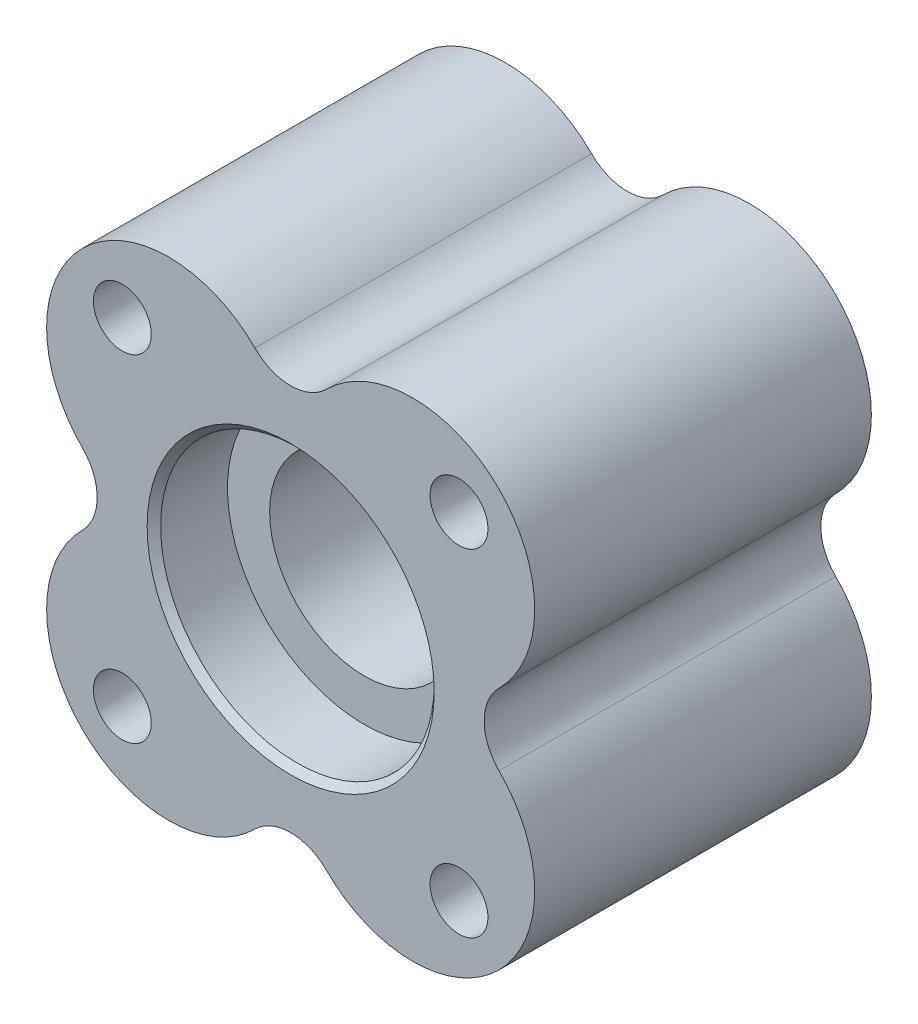
SolidWorks part; units mm, degrees
ref_plane "Front Plane" through (0, 0, 0) normal (0, 0, 1) x (1, 0, 0)
ref_plane "Top Plane" through (0, 0, 0) normal (0, 1, 0) x (1, 0, 0)
ref_plane "Right Plane" through (0, 0, 0) normal (1, 0, 0) x (0, 0, -1)
sketch "Sketch1" plane through (0, 0, 0) normal (0, 0, 1) x (1, 0, 0)
  line L1 (-25.4, 25.4) -> (25.4, 25.4) construction
  line L2 (-25.4, 25.4) -> (-25.4, -25.4) construction
  line L3 (-25.4, -25.4) -> (25.4, -25.4) construction
  line L4 (25.4, 25.4) -> (25.4, -25.4) construction
  line L5 (-25.4, 25.4) -> (25.4, -25.4) construction
  line L6 (-25.4, -25.4) -> (25.4, 25.4) construction
  circle A0 centre (-25.4, 25.4) radius 3.9688
  circle A1 centre (25.4, 25.4) radius 3.9688
  circle A2 centre (25.4, -25.4) radius 3.9688
  circle A3 centre (-25.4, -25.4) radius 3.9688
  circle A4 centre (0, 0) radius 20.6375
  circle A5 centre (0, 0) radius 44.45
  point P0 (0, 0)
  dimension "D3" = 41.275
  dimension "D4" = 7.9375
  dimension "D5" = 88.9
  dimension "D1" = 50.8
  dimension "D2" = 50.8
extrude "Boss-Extrude1" add sketch "Sketch1" along normal mid plane 50.8
sketch "Sketch2" plane through (0, 0, 0) normal (0, 0, 1) x (1, 0, 0)
  circle A0 centre (0, 0) radius 20.6375 construction
  circle A1 centre (0, 0) radius 20.6375
  circle A2 centre (0, 0) radius 14.2875
  dimension "D1" = 6.35
extrude "Boss-Extrude2" add sketch "Sketch2" along normal offset from surface (14.2875 mm away) 11.1125 up to face at (-21.4312, -25.4, 25.4)
sketch "Sketch3" plane through (0, 0, 0) normal (0, 0, -1) x (-1, 0, 0)
  circle A0 centre (0, 0) radius 14.2875 construction
  circle A1 centre (0, 0) radius 20.6375
  circle A2 centre (0, 0) radius 20.6375
  circle A3 centre (0, 0) radius 14.2875
  dimension "D1" = 0
extrude "Boss-Extrude3" add sketch "Sketch3" along normal offset from surface (14.2875 mm away) 11.1125 up to face at (44.45, 0, -25.4)
chamfer "Chamfer1" distance 1.016 angle 45 2 edges at (20.6375, 0, 25.4) (20.6375, 0, -25.4)
sketch "Sketch4" plane through (0, 0, -25.4) normal (0, 0, -1) x (-1, 0, 0)
  line L0 (0, 0) -> (0, 44.45) construction
  line L1 (-18.4118, 18.4118) -> (-25.4, 25.4) construction
  line L2 (0, 0) -> (-18.4118, 18.4118) construction
  arc A0 (-5.3927, 31.4309) -> (-31.4309, 31.4309) centre (-18.4118, 18.4118) ccw
  arc A1 (-5.3927, 31.4309) -> (5.3927, 31.4309) centre (0, 36.8236) ccw
  circle A2 centre (0, 0) radius 44.45 construction
  arc A3 (5.3927, 31.4309) -> (31.4309, 31.4309) centre (18.4118, 18.4118) cw
  arc A4 (31.4309, 31.4309) -> (-31.4309, 31.4309) centre (0, 0) ccw
extrude "Cut-Extrude1" cut sketch "Sketch4" against normal up to next (50.8 mm away)
pattern_circular "CirPattern1" count 4 over 360 about axis through (0, 0, 0) along (0, 0, 1) of "Cut-Extrude1"
hole_wizard "CSK for 5/16 Flat Head Machine Screw (100)1" positions "Sketch5" profile "Sketch6" countersink size "5/16" standard "ANSI Inch" end condition up to next
sketch "Sketch5" plane through (0, 0, -25.4) normal (0, 0, -1) x (-1, 0, 0)
  point P0 (25.4, 25.4)
  point P3 (-25.4, 25.4)
  point P6 (-25.4, -25.4)
  point P9 (25.4, -25.4)
sketch "Sketch6" plane through (-25.4, 25.4, -25.4) normal (1, 0, 0) x (0, 1, 0)
  line L0 (0, 0) -> (0, 50.8)
  line L1 (0, 50.8) -> (4.365, 50.8)
  line L2 (4.365, 50.8) -> (4.365, 3.1043)
  line L3 (4.365, 3.1043) -> (8.0645, 0)
  line L5 (8.0645, 0) -> (0, 0)
  line L6 (-4.365, 3.1043) -> (-8.0645, 0) construction
  line L11 (0, -6.35) -> (0, 107.95) construction
  dimension "Thru Hole Dia." = 8.73
  dimension "Thru Hole Depth" = 50.8
  dimension "Near C'Sink Dia." = 16.129
  dimension "Near C'Sink Angle" = 100
